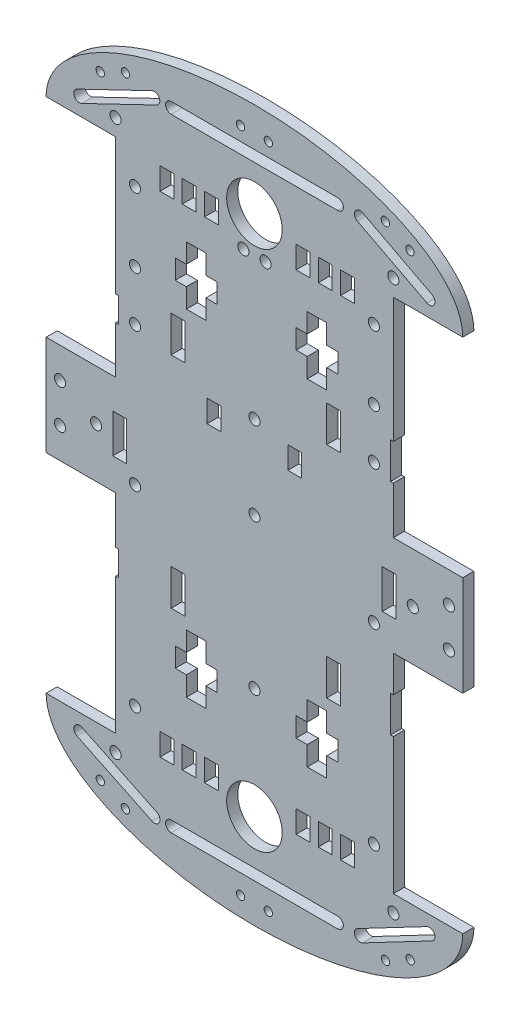
SolidWorks part; units mm, degrees
ref_plane "Front Plane" through (0, 0, 0) normal (0, 0, 1) x (1, 0, 0)
ref_plane "Top Plane" through (0, 0, 0) normal (0, 1, 0) x (1, 0, 0)
ref_plane "Right Plane" through (0, 0, 0) normal (1, 0, 0) x (0, 0, -1)
sketch "Sketch1" plane through (0, 0, 0) normal (0, 0, 1) x (1, 0, 0)
  line L0 (75, 0) -> (-75, 0) construction
  line L1 (0, 94) -> (0, -94) construction
  line L2 (-50, 93) -> (-50, 44)
  line L3 (-50, 18) -> (-75, 18)
  line L4 (-75, 18) -> (-75, -18)
  line L5 (-75, -18) -> (-50, -18)
  line L6 (-50, -18) -> (-50, -35)
  line L8 (50, -18) -> (50, -31)
  line L9 (50, -18) -> (75, -18)
  line L10 (75, -18) -> (75, 18)
  line L11 (75, 18) -> (50, 18)
  line L12 (50, 93) -> (50, 48)
  line L13 (0, 94) -> (0, 138.6441) construction
  line L14 (-75, 93) -> (-50, 93)
  line L15 (50, 93) -> (75, 93)
  line L16 (-75, -93) -> (-50, -93)
  line L17 (50, -93) -> (75, -93)
  line L18 (-50, 44) -> (-49, 44)
  line L19 (-49, 44) -> (-49, 35)
  line L20 (-49, 35) -> (-50, 35)
  line L21 (-50, 35) -> (-50, 18)
  line L22 (50, 48) -> (49, 48)
  line L23 (49, 48) -> (49, 35)
  line L24 (49, 35) -> (50, 35)
  line L25 (50, 35) -> (50, 18)
  line L26 (-50, -35) -> (-49, -35)
  line L27 (-49, -44) -> (-50, -44)
  line L28 (-50, -44) -> (-50, -93)
  line L29 (-49, -35) -> (-49, -44)
  line L30 (-50, -93) -> (50, -93) construction
  line L31 (50, -31) -> (49, -31)
  line L32 (49, -31) -> (49, -44)
  line L33 (49, -44) -> (50, -44)
  line L34 (50, -44) -> (50, -93)
  circle A2 centre (0, 94) radius 10
  circle A3 centre (0, -94) radius 10
  circle A4 centre (0, 0) radius 1.9726
  ellipse E0 centre (0, 93) end of major axis (-75, 93) minor radius 35 (-75, 93) -> (75, 93) cw
  ellipse E1 centre (0, -93) end of major axis (75, -93) minor radius 35 (-75, -93) -> (75, -93) ccw
  point P4 (0, 0)
  point P8 (0, 0)
  point P39 (0, -128)
  point P53 (-50, 93)
extrude "Boss-Extrude2" add sketch "Sketch1" along normal blind 4
sketch "Sketch3" plane through (0, 0, 4) normal (0, 0, 1) x (1, 0, 0)
  circle A0 centre (0, 30) radius 2
  dimension "D1" = 4
  dimension "D2" = 30
extrude "Cut-Extrude1" cut sketch "Sketch3" against normal through all
sketch "Sketch4" plane through (0, 0, 4) normal (0, 0, 1) x (1, 0, 0)
  circle A0 centre (0, -54) radius 2
  dimension "D1" = 4
  dimension "D2" = 54
extrude "Cut-Extrude2" cut sketch "Sketch4" against normal through all
sketch "Sketch5" plane through (0, 0, 0) normal (0, 0, -1) x (-1, 0, 0)
  line L0 (50, 18) -> (75, 18) construction
  line L1 (46, 7) -> (51, 7)
  line L2 (46, 7) -> (46, -7)
  line L3 (46, -7) -> (51, -7)
  line L4 (51, 7) -> (51, -7)
  line L5 (75, 18) -> (75, -18) construction
  dimension "D1" = 5
  dimension "D2" = 14
  dimension "D3" = 11
  dimension "D4" = 11
  dimension "D5" = 29
extrude "Cut-Extrude3" cut sketch "Sketch5" against normal through all
sketch "Sketch6" plane through (0, 0, 0) normal (0, 0, -1) x (-1, 0, 0)
  line L0 (-75, -18) -> (-75, 18) construction
  line L1 (-51, 7) -> (-46, 7)
  line L2 (-51, 7) -> (-51, -7)
  line L3 (-51, -7) -> (-46, -7)
  line L4 (-46, 7) -> (-46, -7)
  line L5 (-50, -18) -> (-75, -18) construction
  line L6 (-75, 18) -> (-50, 18) construction
  dimension "D1" = 5
  dimension "D2" = 14
  dimension "D3" = 29
  dimension "D4" = 11
  dimension "D5" = 11
extrude "Cut-Extrude4" cut sketch "Sketch6" against normal through all
sketch "Sketch7" plane through (0, 0, 0) normal (0, 0, -1) x (-1, 0, 0)
  line L2 (-20, -84) -> (-15, -84)
  line L3 (-20, -84) -> (-20, -91.9813)
  line L4 (-20, -91.9813) -> (-15, -91.9813)
  line L5 (-15, -84) -> (-15, -91.9813)
  point P3 (-0.9699, -84)
extrude "Cut-Extrude6" cut sketch "Sketch7" against normal through all
sketch "Sketch8" plane through (0, 0, 0) normal (0, 0, -1) x (-1, 0, 0)
  line L1 (-23, -83.955) -> (-28, -83.955)
  line L2 (-23, -83.955) -> (-23, -91.955)
  line L3 (-23, -91.955) -> (-28, -91.955)
  line L4 (-28, -83.955) -> (-28, -91.955)
  dimension "D1" = 3
  dimension "D2" = 8
  dimension "D3" = 5
extrude "Cut-Extrude7" cut sketch "Sketch8" against normal through all
sketch "Sketch9" plane through (0, 0, 0) normal (0, 0, -1) x (-1, 0, 0)
  line L1 (-31, -83.955) -> (-36, -83.955)
  line L2 (-31, -83.955) -> (-31, -91.955)
  line L3 (-31, -91.955) -> (-36, -91.955)
  line L4 (-36, -83.955) -> (-36, -91.955)
  dimension "D1" = 8
  dimension "D2" = 8
extrude "Cut-Extrude8" cut sketch "Sketch9" against normal through all
sketch "Sketch10" plane through (0, 0, 0) normal (0, 0, -1) x (-1, 0, 0)
  line L2 (13, -84.4044) -> (18, -84.4044)
  line L3 (13, -84.4044) -> (13, -92.4044)
  line L4 (13, -92.4044) -> (18, -92.4044)
  line L5 (18, -84.4044) -> (18, -92.4044)
  dimension "D1" = 28
  dimension "D2" = 5
  dimension "D3" = 8
extrude "Cut-Extrude9" cut sketch "Sketch10" against normal through all
sketch "Sketch11" plane through (0, 0, 0) normal (0, 0, -1) x (-1, 0, 0)
  line L0 (18, -84.4044) -> (41.6431, -84.4044) construction
  line L2 (21, -84.4044) -> (26, -84.4044)
  line L3 (21, -84.4044) -> (21, -92.4044)
  line L4 (21, -92.4044) -> (26, -92.4044)
  line L5 (26, -84.4044) -> (26, -92.4044)
  dimension "D1" = 8
  dimension "D2" = 3
  dimension "D3" = 5
extrude "Cut-Extrude10" cut sketch "Sketch11" against normal through all
sketch "Sketch12" plane through (0, 0, 0) normal (0, 0, -1) x (-1, 0, 0)
  line L0 (25.4963, -84.4044) -> (40.8921, -84.4044) construction
  line L1 (26, -84.4044) -> (21, -84.4044) construction
  line L3 (29, -84.4044) -> (34, -84.4044)
  line L4 (29, -84.4044) -> (29, -92.4044)
  line L5 (29, -92.4044) -> (34, -92.4044)
  line L6 (34, -84.4044) -> (34, -92.4044)
  dimension "D1" = 8
  dimension "D2" = 5
  dimension "D3" = 3
extrude "Cut-Extrude12" cut sketch "Sketch12" against normal through all
sketch "Sketch13" plane through (0, 0, 0) normal (0, 0, -1) x (-1, 0, 0)
  line L0 (0, 84) -> (46.4499, 84) construction
  line L1 (13, -84.4044) -> (13, 89.8864) construction
  line L3 (13, 84) -> (18, 84)
  line L4 (13, 84) -> (13, 92)
  line L5 (13, 92) -> (18, 92)
  line L6 (18, 84) -> (18, 92)
  circle A0 centre (0, 94) radius 10 construction
  dimension "D1" = 8
  dimension "D2" = 5
extrude "Cut-Extrude13" cut sketch "Sketch13" against normal through all
sketch "Sketch14" plane through (0, 0, 0) normal (0, 0, -1) x (-1, 0, 0)
  line L0 (18, 84) -> (37.1219, 84) construction
  line L2 (21, 84) -> (26, 84)
  line L3 (21, 84) -> (21, 92)
  line L4 (21, 92) -> (26, 92)
  line L5 (26, 84) -> (26, 92)
  dimension "D1" = 8
  dimension "D2" = 3
  dimension "D3" = 5
extrude "Cut-Extrude14" cut sketch "Sketch14" against normal through all
sketch "Sketch15" plane through (0, 0, 0) normal (0, 0, -1) x (-1, 0, 0)
  line L2 (29, 84) -> (34, 84)
  line L3 (29, 84) -> (29, 92)
  line L4 (29, 92) -> (34, 92)
  line L5 (34, 84) -> (34, 92)
  dimension "D1" = 8
  dimension "D2" = 5
extrude "Cut-Extrude15" cut sketch "Sketch15" against normal through all
sketch "Sketch16" plane through (0, 0, 0) normal (0, 0, -1) x (-1, 0, 0)
  line L0 (13, 84) -> (-44.7753, 84) construction
  line L1 (-15, -84) -> (-15, 84) construction
  line L2 (-15, 84) -> (-20, 84)
  line L3 (-15, 84) -> (-15, 92)
  line L4 (-15, 92) -> (-20, 92)
  line L5 (-20, 84) -> (-20, 92)
  dimension "D1" = 28
  dimension "D2" = 8
  dimension "D3" = 5
extrude "Cut-Extrude16" cut sketch "Sketch16" against normal blind 4
sketch "Sketch17" plane through (0, 0, 0) normal (0, 0, -1) x (-1, 0, 0)
  line L0 (-20, 84) -> (-43.1523, 84) construction
  line L2 (-23, 84) -> (-28, 84)
  line L3 (-23, 84) -> (-23, 92)
  line L4 (-23, 92) -> (-28, 92)
  line L5 (-28, 84) -> (-28, 92)
  dimension "D1" = 5
  dimension "D2" = 3
  dimension "D3" = 8
extrude "Cut-Extrude17" cut sketch "Sketch17" against normal through all
sketch "Sketch18" plane through (0, 0, 0) normal (0, 0, -1) x (-1, 0, 0)
  line L0 (-28.0036, 83.9896) -> (-42.6528, 83.9896) construction
  line L2 (-31, 83.9896) -> (-36, 83.9896)
  line L3 (-31, 83.9896) -> (-31, 91.9896)
  line L4 (-31, 91.9896) -> (-36, 91.9896)
  line L5 (-36, 83.9896) -> (-36, 91.9896)
  dimension "D1" = 3
  dimension "D2" = 8
  dimension "D3" = 5
extrude "Cut-Extrude18" cut sketch "Sketch18" against normal through all
sketch "Sketch19" plane through (0, 0, 0) normal (0, 0, -1) x (-1, 0, 0)
  line L0 (0, 0) -> (-85.4788, 0) construction
  line L1 (-51, 7) -> (-51, -7) construction
  circle A0 centre (-57, 0) radius 2
  circle A1 centre (-70, 7.0078) radius 2
  circle A2 centre (-70, -7) radius 2
  point P3 (-57, 0)
  point P4 (-51, 0)
extrude "Cut-Extrude19" cut sketch "Sketch19" against normal through all
sketch "Sketch20" plane through (0, 0, 0) normal (0, 0, -1) x (-1, 0, 0)
  line L0 (0, 0) -> (79.2623, 0) construction
  line L1 (-51, 7) -> (-51, -7) construction
  line L2 (51, -7) -> (51, 7) construction
  line L3 (75, 18) -> (75, -18) construction
  line L4 (50, 18) -> (75, 18) construction
  circle A1 centre (57, 0) radius 2
  circle A2 centre (70, 7) radius 2
  circle A3 centre (70, -7) radius 2
  dimension "D1" = 4
  dimension "D3" = 4
  dimension "D6" = 4
  dimension "D2" = 6
  dimension "D4" = 5
  dimension "D5" = 11
  dimension "D7" = 5
extrude "Cut-Extrude20" cut sketch "Sketch20" against normal through all
sketch "Sketch21" plane through (0, 0, 0) normal (0, 0, -1) x (-1, 0, 0)
  circle A0 centre (4, 81) radius 2
  circle A1 centre (-4, 81) radius 2
  point P4 (0, 81)
  point P8 (0, 81)
  dimension "D1" = 4
  dimension "D3" = 4
  dimension "D4" = 4
  dimension "D2" = 4
extrude "Cut-Extrude21" cut sketch "Sketch21" against normal through all
sketch "Sketch22" plane through (0, 0, 0) normal (0, 0, -1) x (-1, 0, 0)
  line L1 (50, 93) -> (50, 44) construction
  line L2 (-50, 48) -> (-50, 93) construction
  circle A0 centre (43, 81) radius 2
  circle A1 centre (-43, 81) radius 2
  point P5 (4, 81)
  dimension "D1" = 4
  dimension "D3" = 4
  dimension "D2" = 7
  dimension "D4" = 7
extrude "Cut-Extrude22" cut sketch "Sketch22" against normal through all
sketch "Sketch23" plane through (0, 0, 4) normal (0, 0, 1) x (1, 0, 0)
  line L0 (-50, -44) -> (-50, -93) construction
  line L2 (50, -93) -> (50, -44) construction
  circle A0 centre (43, -81) radius 2
  circle A1 centre (-43, -81) radius 2
  point P4 (0.6147, -81)
  point P10 (0.6147, -81)
  dimension "D1" = 4
  dimension "D3" = 4
  dimension "D2" = 7
  dimension "D4" = 7
extrude "Cut-Extrude23" cut sketch "Sketch23" against normal through all
sketch "Sketch24" plane through (0, 0, 4) normal (0, 0, 1) x (1, 0, 0)
  line L0 (50, 93) -> (75, 93) construction
  line L1 (-75, 93) -> (-50, 93) construction
  line L2 (75, -93) -> (50, -93) construction
  line L3 (-50, -93) -> (-75, -93) construction
  line L4 (51, -7) -> (46, -7) construction
  line L5 (-46, -7) -> (-51, -7) construction
  circle A0 centre (-50, -99) radius 2
  circle A1 centre (50, -99) radius 2
  circle A2 centre (-50, 99) radius 2
  circle A3 centre (50, 99) radius 2
  circle A4 centre (43, -12) radius 2
  circle A5 centre (43, 38) radius 2
  circle A6 centre (-43, -12) radius 2
  circle A7 centre (-43, 38) radius 2
  circle A8 centre (43, 56) radius 2
  circle A9 centre (-43, 56) radius 2
  dimension "D1" = 4
  dimension "D2" = 4
  dimension "D3" = 4
  dimension "D4" = 4
  dimension "D5" = 4
  dimension "D6" = 4
  dimension "D7" = 4
  dimension "D8" = 4
  dimension "D9" = 4
  dimension "D10" = 4
  dimension "D11" = 6
  dimension "D12" = 6
  dimension "D13" = 6
  dimension "D14" = 6
  dimension "D15" = 5
  dimension "D16" = 5
  dimension "D17" = 50
  dimension "D18" = 50
  dimension "D19" = 18
  dimension "D20" = 18
extrude "Cut-Extrude24" cut sketch "Sketch24" against normal through all
sketch "Sketch25" plane through (0, 0, 0) normal (0, 0, -1) x (-1, 0, 0)
  line L1 (-31, 48) -> (-31, 34.3887) construction
  line L5 (-31, 48) -> (-26, 48)
  line L6 (-31, 48) -> (-31, 35)
  line L7 (-31, 35) -> (-26, 35)
  line L8 (-26, 48) -> (-26, 35)
  line L12 (25, 48) -> (30, 48)
  line L13 (25, 48) -> (25, 35)
  line L14 (25, 35) -> (30, 35)
  line L15 (30, 48) -> (30, 35)
  line L22 (-31, -31) -> (-26, -31)
  line L23 (-31, -31) -> (-31, -44)
  line L24 (-31, -44) -> (-26, -44)
  line L25 (-26, -31) -> (-26, -44)
  line L26 (25, -31) -> (30, -31)
  line L27 (25, -31) -> (25, -44)
  line L28 (25, -44) -> (30, -44)
  line L29 (30, -31) -> (30, -44)
  dimension "D2" = 5
  dimension "D5" = 5
  dimension "D7" = 5
  dimension "D8" = 5
extrude "Cut-Extrude25" cut sketch "Sketch25" against normal through all
sketch "Sketch26" plane through (0, 0, 0) normal (0, 0, -1) x (-1, 0, 0)
  line L0 (24.5102, 52) -> (17.5102, 52)
  line L1 (24.5102, 52) -> (24.5102, 59) construction
  line L2 (-26, 73) -> (-19, 73) construction
  line L3 (17.5102, 52) -> (17.5102, 59)
  line L4 (17.5102, 59) -> (13.5102, 59)
  line L5 (-30, 59) -> (-30, 66)
  line L6 (13.5102, 59) -> (13.5102, 66)
  line L7 (-15, 66) -> (-15, 59)
  line L8 (13.5102, 66) -> (17.5102, 66)
  line L9 (-26, 52) -> (-19, 52)
  line L10 (-19, 52) -> (-19, 59)
  line L11 (-19, 59) -> (-15, 59)
  line L12 (-15, 66) -> (-19, 66)
  line L13 (-19, 66) -> (-19, 73)
  line L14 (-19, 73) -> (-26, 73)
  line L15 (-26, 73) -> (-26, 66)
  line L16 (-26, 66) -> (-30, 66)
  line L17 (-30, 59) -> (-26, 59)
  line L18 (-26, 59) -> (-26, 52)
  line L19 (17.5102, 66) -> (17.5102, 73)
  line L20 (17.5102, 73) -> (24.5102, 73)
  line L21 (24.5102, 73) -> (24.5102, 66)
  line L22 (24.5102, 66) -> (28.5102, 66)
  line L23 (28.5102, 66) -> (28.5102, 59)
  line L24 (28.5102, 59) -> (24.5102, 59)
  line L35 (24.5102, 59) -> (24.5102, 52)
  line L36 (-19, -69) -> (-19, -62)
  line L37 (-26, -48) -> (-19, -48)
  line L38 (-19, -48) -> (-19, -55)
  line L39 (-19, -55) -> (-15, -55)
  line L40 (-15, -55) -> (-15, -62)
  line L41 (-15, -62) -> (-19, -62)
  line L42 (-19, -69) -> (-26, -69)
  line L43 (-26, -69) -> (-26, -62)
  line L44 (-26, -62) -> (-30, -62)
  line L45 (-30, -62) -> (-30, -55)
  line L46 (-30, -55) -> (-26, -55)
  line L47 (-26, -55) -> (-26, -48)
  line L49 (24.5102, -48) -> (17.5102, -48)
  line L50 (17.5102, -48) -> (17.5102, -55)
  line L51 (17.5102, -55) -> (13.5102, -55)
  line L52 (13.5102, -55) -> (13.5102, -62)
  line L53 (13.5102, -62) -> (17.5102, -62)
  line L54 (17.5102, -62) -> (17.5102, -69)
  line L55 (17.5102, -69) -> (24.5102, -69)
  line L56 (24.5102, -69) -> (24.5102, -62)
  line L57 (24.5102, -62) -> (28.5102, -62)
  line L58 (28.5102, -62) -> (28.5102, -55)
  line L59 (28.5102, -55) -> (24.5102, -55)
  line L60 (24.5102, -55) -> (24.5102, -48)
  point P26 (-26, -48)
extrude "Cut-Extrude26" cut sketch "Sketch26" against normal through all
sketch "Sketch27" plane through (0, 0, 0) normal (0, 0, -1) x (-1, 0, 0)
  line L4 (-12, 28) -> (-17, 28)
  line L5 (-12, 28) -> (-12, 20)
  line L6 (-12, 20) -> (-17, 20)
  line L7 (-17, 28) -> (-17, 20)
  line L8 (12.026, 28) -> (17.026, 28)
  line L9 (12.026, 28) -> (12.026, 20)
  line L10 (12.026, 20) -> (17.026, 20)
  line L11 (17.026, 28) -> (17.026, 20)
  point P4 (-12, 28)
  point P6 (12, 28)
extrude "Cut-Extrude27" cut sketch "Sketch27" against normal through all
sketch "Sketch28" plane through (0, 0, 0) normal (0, 0, -1) x (-1, 0, 0)
  line L1 (30, -112) -> (-30, -112)
  line L2 (-30, 112) -> (30, 112) construction
  line L3 (-30, 114) -> (30, 114)
  line L4 (-30, 110) -> (30, 110)
  line L5 (-30, -112) -> (30, -112) construction
  line L6 (-30, -110) -> (30, -110)
  line L7 (-30, -114) -> (30, -114)
  line L8 (-63, 99) -> (-38, 112) construction
  line L9 (-63.9227, 100.7744) -> (-38.9227, 113.7744)
  line L10 (-62.0773, 97.2256) -> (-37.0773, 110.2256)
  line L11 (36.0632, 112.09) -> (63.0485, 99.1007) construction
  line L12 (36.9306, 113.8921) -> (63.9159, 100.9028)
  line L13 (35.1957, 110.2879) -> (62.1811, 97.2986)
  line L21 (36, -112) -> (63, -99) construction
  line L22 (35.1324, -110.198) -> (62.1324, -97.198)
  line L23 (36.8676, -113.802) -> (63.8676, -100.802)
  line L24 (-63, -99) -> (-38, -112.1208) construction
  line L25 (-62.0706, -97.2291) -> (-37.0706, -110.3499)
  line L26 (-63.9294, -100.7709) -> (-38.9294, -113.8918)
  arc A0 (-30, 114) -> (-30, 110) centre (-30, 112) ccw
  arc A1 (30, 110) -> (30, 114) centre (30, 112) ccw
  arc A2 (-63.9227, 100.7744) -> (-62.0773, 97.2256) centre (-63, 99) ccw
  arc A4 (-37.0773, 110.2256) -> (-38.9227, 113.7744) centre (-38, 112) ccw
  arc A5 (36.9306, 113.8921) -> (35.1957, 110.2879) centre (36.0632, 112.09) ccw
  arc A6 (62.1811, 97.2986) -> (63.9159, 100.9028) centre (63.0485, 99.1007) ccw
  arc A7 (35.1324, -110.198) -> (36.8676, -113.802) centre (36, -112) ccw
  arc A8 (-30, -110) -> (-30, -114) centre (-30, -112) ccw
  arc A9 (30, -114) -> (30, -110) centre (30, -112) ccw
  arc A11 (63.8676, -100.802) -> (62.1324, -97.198) centre (63, -99) ccw
  arc A12 (-62.0706, -97.2291) -> (-63.9294, -100.7709) centre (-63, -99) ccw
  arc A13 (-38.9294, -113.8918) -> (-37.0706, -110.3499) centre (-38, -112.1208) ccw
  point P4 (0, -112)
  point P6 (0, -112)
  point P10 (0, 112)
  point P15 (-36, -112)
  point P16 (0, -112)
  point P22 (-30, -112)
  point P23 (-38, -112.1208)
  point P25 (63.0485, 99.1007)
  point P26 (-38, 112)
  point P29 (-50.5, 105.5)
  point P35 (34, -112)
  point P36 (36.0632, 112.09)
  point P39 (49.5558, 105.5954)
  point P44 (30, -112)
  point P57 (36, -112)
  point P60 (49.5, -105.5)
  point P65 (-50.5, -105.5604)
extrude "Cut-Extrude29" cut sketch "Sketch28" against normal through all contours L9 A4 L10 A2 | L3 A1 L4 A0 | L12 A6 L13 A5 | L26 A13 L25 A12 | L7 A9 L6 A8 | L23 A11 L22 A7
sketch "Sketch29" plane through (0, 0, 0) normal (0, 0, -1) x (-1, 0, 0)
  circle A0 centre (5, 119) radius 1.5
  circle A1 centre (-5, 119) radius 1.5
  circle A2 centre (55.5065, 110.4998) radius 1.5
  circle A3 centre (46.4485, 114.7369) radius 1.5
  circle A4 centre (-55.9965, 110.5317) radius 1.5
  circle A5 centre (-47.1243, 115.1452) radius 1.5
  circle A6 centre (5, -121) radius 1.5
  circle A7 centre (-5, -121) radius 1.5
  circle A8 centre (55.4833, -110.3883) radius 1.5
  circle A9 centre (46.4732, -114.7265) radius 1.5
  circle A10 centre (-47.206, -115.1947) radius 1.5
  circle A11 centre (-56.0605, -110.5476) radius 1.5
  point P7 (5, 119)
extrude "Cut-Extrude30" cut sketch "Sketch29" against normal through all
